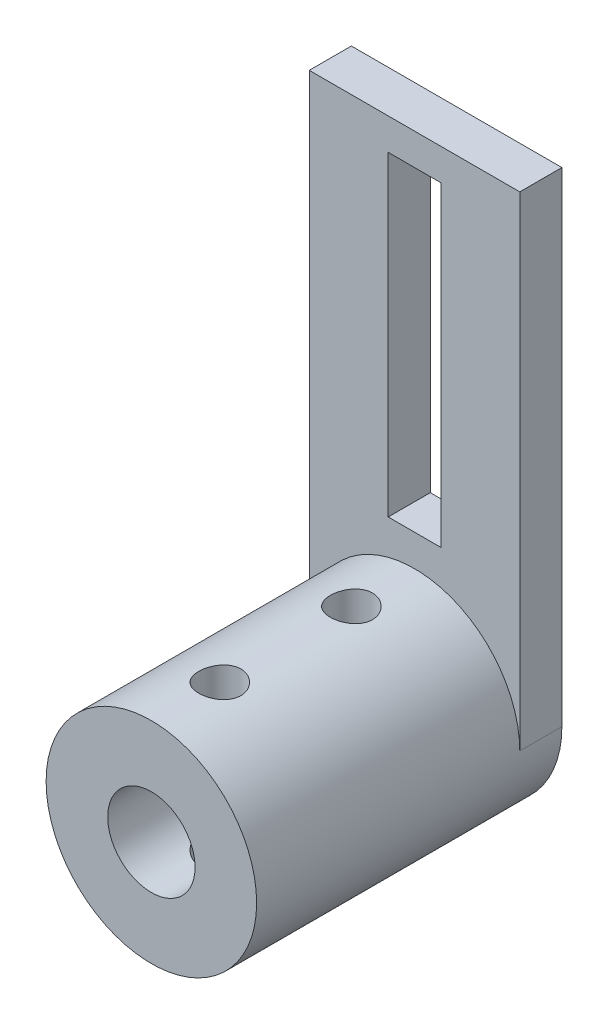
SolidWorks part; units mm, degrees
ref_plane "Alzado" through (0, 0, 0) normal (0, 0, 1) x (1, 0, 0)
ref_plane "Planta" through (0, 0, 0) normal (0, 1, 0) x (1, 0, 0)
ref_plane "Vista lateral" through (0, 0, 0) normal (1, 0, 0) x (0, 0, -1)
sketch "Croquis1" plane through (0, 0, 0) normal (0, 0, 1) x (1, 0, 0)
  line L1 (2.5, -5) -> (-2.5, -5)
  line L2 (10, -18) -> (10, 28)
  line L3 (10, 28) -> (-10, 28)
  line L4 (-10, -18) -> (-10, 28)
  line L5 (10, -28) -> (-10, 28) construction
  line L6 (10, 28) -> (-10, -28) construction
  line L7 (2.5, -5) -> (2.5, 25)
  line L8 (2.5, 25) -> (-2.5, 25)
  line L9 (-2.5, -5) -> (-2.5, 25)
  line L10 (2.5, -5) -> (-2.5, 25) construction
  line L11 (2.5, 25) -> (-2.5, -5) construction
  arc A0 (-10, -18) -> (10, -18) centre (0, -18) ccw
  point P0 (0, 0)
  point P7 (0, 10)
  dimension "D1" = 20
  dimension "D3" = 10
  dimension "D4" = 20
extrude "Saliente-Extruir1" add sketch "Croquis1" along normal blind 4
sketch "Croquis2" plane through (0, 0, 0) normal (0, 0, 1) x (1, 0, 0)
  circle A0 centre (0, -18) radius 10
  arc A1 (-10, -18) -> (10, -18) centre (0, -18) ccw construction
  circle A2 centre (0, -18) radius 4.15
  dimension "D1" = 20
  dimension "D3" = 8.3
  dimension "D2" = 0
extrude "Saliente-Extruir2" add sketch "Croquis2" along normal blind 25 from surface at 4 starting at face at (0, 2.5, 4)
sketch "Croquis3" plane through (0, 0, 0) normal (0, 0, 1) x (1, 0, 0)
  circle A0 centre (0, -18) radius 4.15
extrude "Cortar-Extruir1" cut sketch "Croquis3" against normal up to surface (4 mm away) from surface at 4 up to face at (0, 2.5, 0) starting at face at (4.15, -18, 4)
sketch "Croquis4" plane through (0, 0, 0) normal (0, 1, 0) x (1, 0, 0)
  circle A0 centre (0, -10) radius 2
  circle A1 centre (0, -22.5) radius 2
  dimension "D1" = 4
  dimension "D2" = 4
extrude "Cortar-Extruir2" cut sketch "Croquis4" against normal through all
